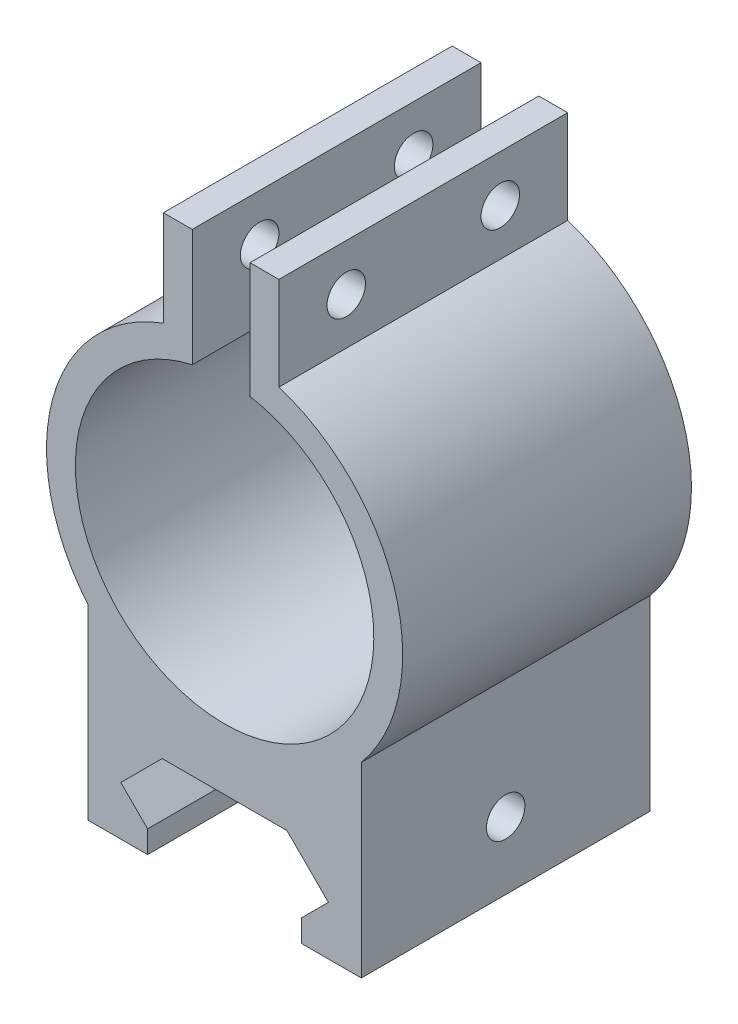
SolidWorks part; units mm, degrees
ref_plane "Front Plane" through (0, 0, 0) normal (0, 0, 1) x (1, 0, 0)
ref_plane "Top Plane" through (0, 0, 0) normal (0, 1, 0) x (1, 0, 0)
ref_plane "Right Plane" through (0, 0, 0) normal (1, 0, 0) x (0, 0, -1)
sketch "Sketch1" plane through (0, 0, 0) normal (0, 0, 1) x (1, 0, 0)
  line L0 (2.6406, 55.0585) -> (2.6406, 61.0719)
  line L1 (2.6406, 61.0719) -> (5.6406, 61.0719)
  line L2 (5.6406, 61.0719) -> (5.6406, 51.377)
  line L3 (-3.3594, 55.0692) -> (-3.3594, 48.8895)
  line L4 (11.0828, 2.5) -> (8, 2.5)
  line L5 (8, 2.5) -> (8, 4.8172)
  line L6 (8, 4.8172) -> (10.7828, 7.6)
  line L7 (10.7828, 7.6) -> (6.4828, 11.9)
  line L8 (6.4828, 11.9) -> (-6.4828, 11.9)
  line L9 (-6.4828, 11.9) -> (-10.7828, 7.6)
  line L10 (-10.7828, 7.6) -> (-8, 4.8172)
  line L11 (-8, 4.8172) -> (-8, 2.5)
  line L12 (-8, 2.5) -> (-11.0828, 2.5)
  line L13 (-3.3594, 55.0692) -> (-3.3594, 61.0692)
  line L14 (2.6406, 55.0585) -> (2.6406, 49.0313)
  line L15 (-3.3594, 61.0692) -> (-6.3594, 61.0692)
  line L16 (-6.3594, 61.0692) -> (-6.3594, 51.1305)
  line L19 (-11.0828, 2.5) -> (-14.2, 2.5)
  line L20 (11.0828, 2.5) -> (14.2, 2.5)
  line L21 (14.2, 2.5) -> (14.2, 21.9)
  line L22 (-14.2, 2.5) -> (-14.2, 21.9)
  arc A1 (14.2, 21.9) -> (5.6406, 51.377) centre (0, 33.7579) ccw
  arc A2 (-3.3594, 48.8895) -> (2.6406, 49.0313) centre (0, 33.7579) ccw
  arc A3 (-6.3594, 51.1305) -> (-14.2, 21.9) centre (0, 33.7579) ccw
  point P0 (0, 11.9)
  point P2 (2.5, 75.5053)
  point P3 (-0.3594, 55.0013)
  point P5 (-2.5, 75.5053)
  dimension "D1" = 3
  dimension "D3" = 3
  dimension "D4" = 3
  dimension "D6" = 15.5
  dimension "D2" = 3
  dimension "D5" = 3
extrude "Boss-Extrude1" add sketch "Sketch1" along normal blind 30
sketch "Sketch2" plane through (5.6406, 0, 0) normal (1, 0, 0) x (0, 0, -1)
  line L0 (-30, 61.0719) -> (0, 61.0719) construction
  line L1 (-30, 51.377) -> (0, 51.377) construction
  line L2 (0, 51.377) -> (0, 61.0719) construction
  line L3 (-30, 51.377) -> (-30, 61.0719) construction
  circle A0 centre (-7, 56.2245) radius 2
  circle A1 centre (-23, 56.2245) radius 2
  point P0 (-15, 61.0719)
  point P1 (-15, 51.377)
  point P4 (0, 56.2245)
  point P7 (-30, 56.2245)
  dimension "D1" = 8
  dimension "D2" = 8
extrude "Cut-Extrude1" cut sketch "Sketch2" against normal through all
sketch "Sketch3" plane through (14.2, 0, 0) normal (1, 0, 0) x (0, 0, -1)
  line L0 (0, 2.5) -> (0, 21.9) construction
  circle A0 centre (-15, 9.5) radius 2
  point P0 (0, 7.6)
  dimension "D1" = 15
  dimension "D2" = 7
extrude "Cut-Extrude2" cut sketch "Sketch3" against normal through all contours A0
